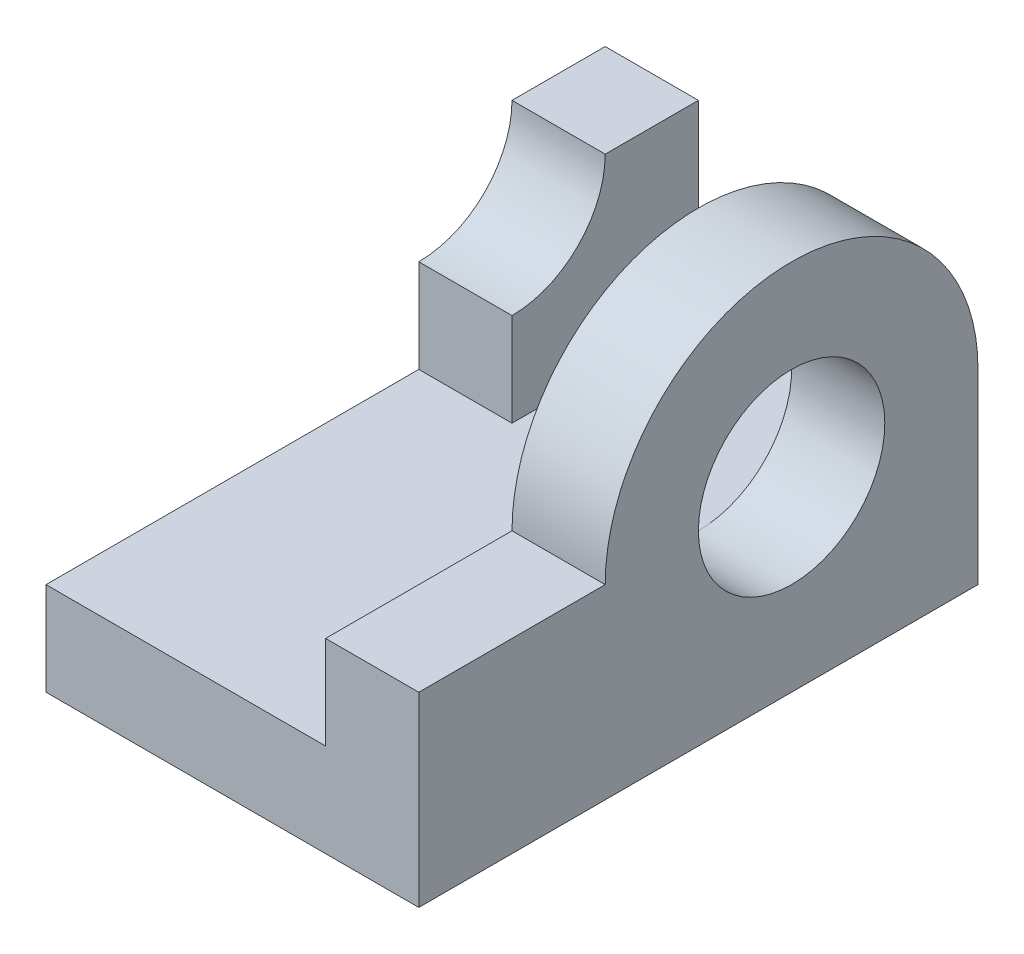
SolidWorks part; units mm, degrees
material "Aleación 1060"
ref_plane "Alzado" through (0, 0, 0) normal (0, 0, 1) x (1, 0, 0)
ref_plane "Planta" through (0, 0, 0) normal (0, 1, 0) x (1, 0, 0)
ref_plane "Vista lateral" through (0, 0, 0) normal (1, 0, 0) x (0, 0, -1)
sketch "Croquis1" plane through (0, 0, 0) normal (1, 0, 0) x (0, 0, -1)
  line L0 (-20, 0) -> (-40, 0)
  line L1 (-40, 0) -> (-40, -20)
  line L2 (-40, -20) -> (0, -20)
  circle A0 centre (0, 0) radius 20
  circle A1 centre (0, 0) radius 10
extrude "Saliente-Extruir1" add sketch "Croquis1" along normal blind 10 contours A0 A1 | A0 L0 L1 L2
sketch "Croquis2" plane through (0, 0, 0) normal (-1, 0, 0) x (0, 0, 1)
  line L0 (-20, -10) -> (-20, 0)
  line L5 (40, -20) -> (-20, -20)
  line L6 (40, -20) -> (40, -10)
  line L7 (40, -10) -> (-20, -10)
  line L8 (-20, -20) -> (-20, -10)
  line L9 (-20, 0) -> (-17.3205, -10)
  line L10 (-17.3205, -10) -> (-20, -10)
  arc A0 (20, 0) -> (0, -20) centre (0, 0) ccw construction
  arc M9 (20, 0) -> (0, -20) centre (0, 0) ccw
  line M10 (0, -20) -> (40, -20)
  line M11 (40, -20) -> (40, 0)
  dimension "D1" = 10
  dimension "D2" = 60
extrude "Saliente-Extruir2" add sketch "Croquis2" along normal blind 30 contours L8 L5 L7 M9 | L7 M11 M9 M10
sketch "Croquis3" plane through (10, 0, 0) normal (1, 0, 0) x (0, 0, -1)
  line L0 (0, -20) -> (20, -20)
  line L1 (20, -20) -> (20, 0)
  line L2 (20, 0) -> (0, -20)
  arc A0 (0, -20) -> (-20, 0) centre (0, 0) ccw construction
extrude "Saliente-Extruir3" add sketch "Croquis3" against normal blind 10
sketch "Croquis4" plane through (-30, 0, 0) normal (-1, 0, 0) x (0, 0, 1)
  line L0 (-20, -10) -> (-20, 10)
  line L1 (-20, 10) -> (-10, 10)
  line L2 (-10, 10) -> (-10, 0) construction
  line L3 (-10, 0) -> (0, 0) construction
  line L4 (0, 0) -> (0, -10)
  line L5 (40, -10) -> (-20, -10) construction
  line L6 (0, -10) -> (-20, -10)
  circle A0 centre (0, 0) radius 10 construction
  arc A1 (0, 0) -> (-10, 10) centre (0, 10) cw
extrude "Saliente-Extruir4" add sketch "Croquis4" against normal blind 10
